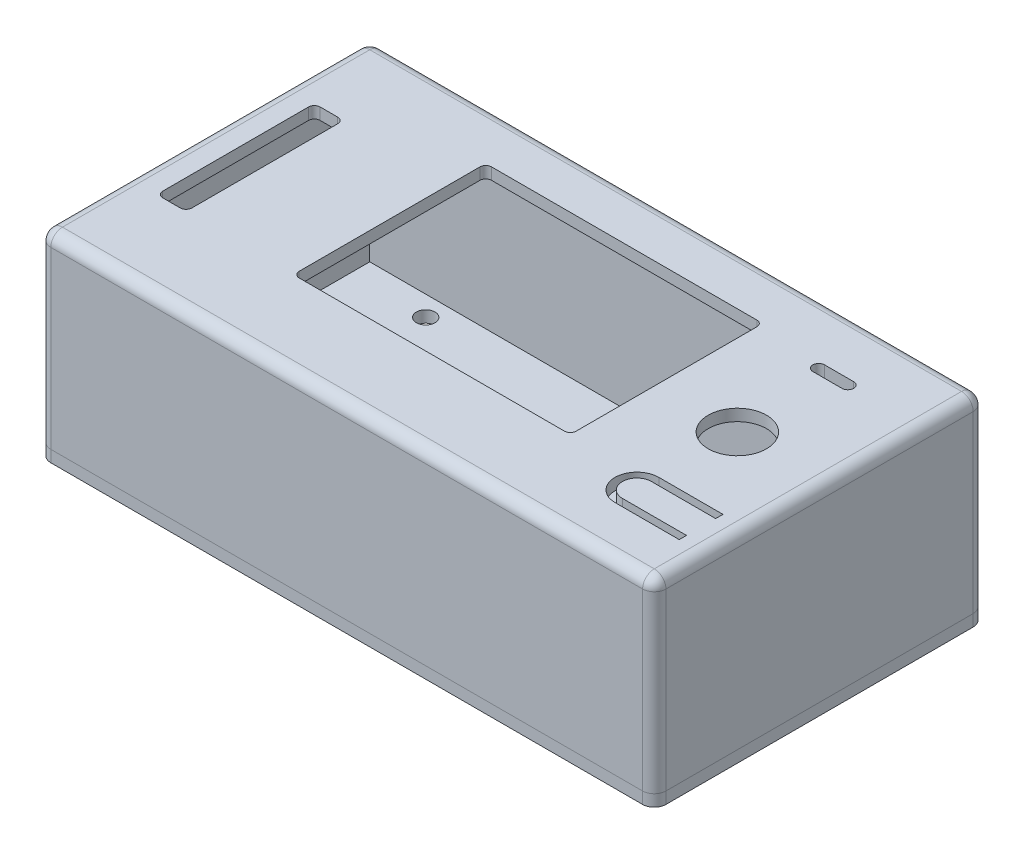
SolidWorks part; units mm, degrees
ref_plane "Alzado" through (0, 0, 0) normal (0, 0, 1) x (1, 0, 0)
ref_plane "Planta" through (0, 0, 0) normal (0, 1, 0) x (1, 0, 0)
ref_plane "Vista lateral" through (0, 0, 0) normal (1, 0, 0) x (0, 0, -1)
sketch "Croquis1" plane through (0, 0, 0) normal (0, 1, 0) x (1, 0, 0)
  line L0 (-2.25, 54.45) -> (103.25, 54.45)
  line L1 (0, 0) -> (101, 0) construction
  line L2 (0, 0) -> (0, 52.2) construction
  line L3 (0, 52.2) -> (101, 52.2) construction
  line L4 (101, 0) -> (101, 52.2) construction
  line L5 (26.6, 45.5) -> (74.1, 45.5)
  line L6 (26.6, 45.5) -> (26.6, 12.5)
  line L7 (26.6, 12.5) -> (74.1, 12.5)
  line L8 (74.1, 45.5) -> (74.1, 12.5)
  line L9 (3, 39.7) -> (8, 39.7)
  line L10 (3, 39.7) -> (3, 12.7)
  line L11 (3, 12.7) -> (8, 12.7)
  line L12 (8, 39.7) -> (8, 12.7)
  line L13 (103.25, -2.25) -> (103.25, 54.45)
  line L14 (-2.25, -2.25) -> (103.25, -2.25)
  line L15 (-2.25, -2.25) -> (-2.25, 54.45)
  line L16 (88.05, 12.48) -> (99.05, 12.48)
  line L17 (88.05, 7.48) -> (99.05, 7.48)
  line L18 (88.05, 6.23) -> (99.05, 6.23)
  line L19 (88.05, 13.73) -> (99.05, 13.73)
  line L20 (99.05, 13.73) -> (99.05, 12.48)
  line L21 (99.05, 7.48) -> (99.05, 6.23)
  line L22 (90.55, 43.65) -> (85.55, 43.65) construction
  line L23 (90.55, 42.65) -> (85.55, 42.65)
  line L24 (90.55, 44.65) -> (85.55, 44.65)
  line L25 (-0.75, -0.75) -> (101.75, -0.75) construction
  line L26 (101.75, -0.75) -> (101.75, 52.95) construction
  line L27 (-0.75, 52.95) -> (101.75, 52.95) construction
  line L28 (-0.75, -0.75) -> (-0.75, 52.95) construction
  circle A0 centre (98.3, 49.5) radius 1.6 construction
  circle A1 centre (98.3, 2.7) radius 1.6 construction
  circle A2 centre (12.3, 49.5) radius 1.6 construction
  circle A3 centre (12.3, 2.7) radius 1.6 construction
  circle A4 centre (88.05, 27.2) radius 5
  circle A5 centre (88.05, 43.65) radius 3 construction
  arc A6 (88.05, 12.48) -> (88.05, 7.48) centre (88.05, 9.98) ccw
  arc A7 (88.05, 13.73) -> (88.05, 6.23) centre (88.05, 9.98) ccw
  arc A8 (90.55, 42.65) -> (90.55, 44.65) centre (90.55, 43.65) ccw
  arc A9 (85.55, 44.65) -> (85.55, 42.65) centre (85.55, 43.65) ccw
  point P41 (88.05, 43.65)
  dimension "D3" = 3.2
  dimension "D6" = 2.7
  dimension "D12" = 10
  dimension "D15" = 6
  dimension "D17" = 5
  dimension "D1" = 52.2
  dimension "D2" = 101
  dimension "D4" = 46.8
  dimension "D5" = 2.7
  dimension "D7" = 86
  dimension "D8" = 47.5
  dimension "D9" = 33
  dimension "D10" = 12.5
  dimension "D11" = 26.9
  dimension "D13" = 12.95
  dimension "D14" = 25
  dimension "D16" = 8.55
  dimension "D18" = 17.22
  dimension "D19" = 27
  dimension "D20" = 5
  dimension "D21" = 12.5
  dimension "D22" = 8
  dimension "D24" = 11
  dimension "D25" = 1.25
  dimension "D26" = 5
  dimension "D27" = 2
  dimension "D23" = 1.5
  dimension "D28" = 0.75
extrude "Saliente-Extruir1" add sketch "Croquis1" along normal blind 2
sketch "Croquis5" plane through (0, 0, 0) normal (0, -1, 0) x (1, 0, 0)
  line L8 (-2.25, 2.25) -> (-2.25, -54.45) construction
  line L9 (-2.25, 2.25) -> (103.25, 2.25) construction
  line L10 (103.25, 2.25) -> (103.25, -54.45) construction
  line L11 (-2.25, -54.45) -> (103.25, -54.45) construction
  line L12 (-2.25, 2.25) -> (-2.25, -54.45)
  line L13 (-2.25, 2.25) -> (103.25, 2.25)
  line L14 (103.25, 2.25) -> (103.25, -54.45)
  line L15 (-2.25, -54.45) -> (103.25, -54.45)
  line L16 (101.75, 0.75) -> (101.75, -52.95) construction
  line L17 (-0.75, 0.75) -> (101.75, 0.75) construction
  line L18 (-0.75, 0.75) -> (-0.75, -52.95) construction
  line L19 (-0.75, -52.95) -> (101.75, -52.95) construction
  line L20 (101.75, 0.75) -> (101.75, -52.95)
  line L21 (-0.75, 0.75) -> (101.75, 0.75)
  line L22 (-0.75, 0.75) -> (-0.75, -52.95)
  line L23 (-0.75, -52.95) -> (101.75, -52.95)
extrude "Saliente-Extruir4" add sketch "Croquis5" along normal blind 30
sketch "Croquis6" plane through (0, -30, 0) normal (0, -1, 0) x (1, 0, 0)
  line L0 (103.25, 2.25) -> (103.25, -54.45) construction
  line L1 (-2.25, 2.25) -> (103.25, 2.25) construction
  line L2 (-2.25, 2.25) -> (-2.25, -54.45) construction
  line L3 (-2.25, -54.45) -> (103.25, -54.45) construction
  line L4 (103.25, 2.25) -> (103.25, -54.45)
  line L5 (-2.25, 2.25) -> (103.25, 2.25)
  line L6 (-2.25, 2.25) -> (-2.25, -54.45)
  line L7 (-2.25, -54.45) -> (103.25, -54.45)
  line L8 (50.5, 2.25) -> (50.5, -54.45) construction
  line L10 (40.75, -10.75) -> (19.75, -10.75)
  line L11 (42.75, -8.75) -> (42.75, -2.75)
  line L12 (40.75, -0.75) -> (19.75, -0.75)
  line L13 (17.75, -8.75) -> (17.75, -2.75)
  circle A0 centre (98.3, -2.7) radius 1.6 construction
  circle A1 centre (12.3, -49.5) radius 1.6 construction
  circle A2 centre (12.3, -49.5) radius 1.6
  circle A3 centre (98.3, -49.5) radius 1.6 construction
  circle A4 centre (98.3, -2.7) radius 1.6
  circle A7 centre (98.3, -49.5) radius 1.6
  arc A10 (42.75, -2.75) -> (40.75, -0.75) centre (40.75, -2.75) ccw
  arc A11 (40.75, -10.75) -> (42.75, -8.75) centre (40.75, -8.75) ccw
  arc A12 (19.75, -10.75) -> (17.75, -8.75) centre (19.75, -8.75) cw
  arc A13 (19.75, -0.75) -> (17.75, -2.75) centre (19.75, -2.75) ccw
  circle A14 centre (12.3, -2.7) radius 1.6 construction
  circle A15 centre (12.3, -2.7) radius 1.6
  point P22 (42.75, -0.75)
  point P25 (42.75, -10.75)
  point P30 (17.75, -0.75)
  dimension "D5" = 2
  dimension "D1" = 25
  dimension "D2" = 10
  dimension "D3" = 20
  dimension "D4" = 3
extrude "Saliente-Extruir5" add sketch "Croquis6" along normal blind 2
ref_plane "Plano1" through (0, -30, 0) normal (0, -1, 0) x (-1, 0, 0)
sketch "Croquis8" plane through (0, 0, 0) normal (0, -1, 0) x (1, 0, 0)
  line L0 (0, 0) -> (101, 0) construction
  line L2 (9.225, 0.75) -> (9.225, -6.25)
  line L3 (9.225, -6.25) -> (15.375, -6.25)
  line L4 (15.375, 0.75) -> (15.375, -6.25)
  line L5 (101, -26.1) -> (-2.25, -26.1) construction
  line L6 (101, 0) -> (101, -52.2) construction
  line L7 (-2.25, 2.25) -> (-2.25, -54.45) construction
  line L8 (50.5, 0) -> (50.5, -52.2) construction
  line L9 (0, -52.2) -> (101, -52.2) construction
  line L17 (101.75, -6.25) -> (95.6, -6.25)
  line L18 (95.6, 0.75) -> (95.6, -6.25)
  line L23 (101.75, 0.75) -> (101.75, -52.95) construction
  line L24 (-0.75, 0.75) -> (101.75, 0.75) construction
  line L25 (95.6, 0.75) -> (101.75, 0.75)
  line L26 (101.75, 0.75) -> (101.75, -6.25)
  line L27 (9.225, 0.75) -> (15.375, 0.75)
  line L28 (9.225, -52.95) -> (15.375, -52.95)
  line L29 (15.375, -52.95) -> (15.375, -45.95)
  line L30 (9.225, -45.95) -> (15.375, -45.95)
  line L31 (9.225, -52.95) -> (9.225, -45.95)
  line L32 (101.75, -52.95) -> (101.75, -45.95)
  line L33 (95.6, -52.95) -> (101.75, -52.95)
  line L34 (101.75, -45.95) -> (95.6, -45.95)
  line L35 (95.6, -52.95) -> (95.6, -45.95)
  dimension "D1" = 6.15
  dimension "D2" = 7
  dimension "D3" = 3.075
  dimension "D4" = 7
  dimension "D5" = 6.15
extrude "Saliente-Extruir13" add sketch "Croquis8" along normal blind 9
sketch "Croquis9" plane through (0, -9, 0) normal (0, -1, 0) x (1, 0, 0)
  circle A0 centre (12.3, -2.7) radius 2.15
  circle A1 centre (98.3, -2.7) radius 2.15
  circle A2 centre (98.3, -49.5) radius 2.15
  circle A3 centre (12.3, -49.5) radius 2.15
  dimension "D1" = 4.3
extrude "Cortar-Extruir2" cut sketch "Croquis9" against normal blind 3.5
fillet "Redondeo4" radius 2 8 edges at (103.25, -15, -54.45) (-2.25, -15, -54.45) (-2.25, -15, 2.25) (-2.25, 2, -26.1) (50.5, 2, -54.45) (103.25, 2, -26.1) (50.5, 2, 2.25) (103.25, -15, 2.25)
split "Partir1" trim tools "Plano1" bodies to split 108 resulting bodies 111 112
fillet "Redondeo6" radius 1 8 edges at (8, 1, -39.7) (3, 1, -39.7) (3, 1, -12.7) (8, 1, -12.7) (26.6, 1, -12.5) (74.1, 1, -12.5) (74.1, 1, -45.5) (26.6, 1, -45.5)
fillet "Redondeo7" radius 1 18 edges at (101.75, -4.5, -6.25) (100.4, 0, -6.25) (95.6, 0, -2.74) (95.6, -4.5, 0.75) (9.225, -4.5, 0.75) (9.225, 0, -2.75) (12.3, 0, -6.25) (15.375, 0, -2.75) (15.375, -4.5, 0.75) (9.225, -4.5, -52.95) (9.225, 0, -49.45) (12.3, 0, -45.95) (15.375, 0, -49.45) (15.375, -4.5, -52.95) (95.6, -4.5, -52.95) (101.75, -4.5, -45.95) (98.675, 0, -45.95) (95.6, 0, -49.45)
sketch "Croquis10" plane through (0, 0, 0) normal (0, -1, 0) x (1, 0, 0)
  circle A0 centre (88.05, -9.98) radius 2.5
extrude "Saliente-Extruir14" add sketch "Croquis10" along normal blind 2 contours A0
